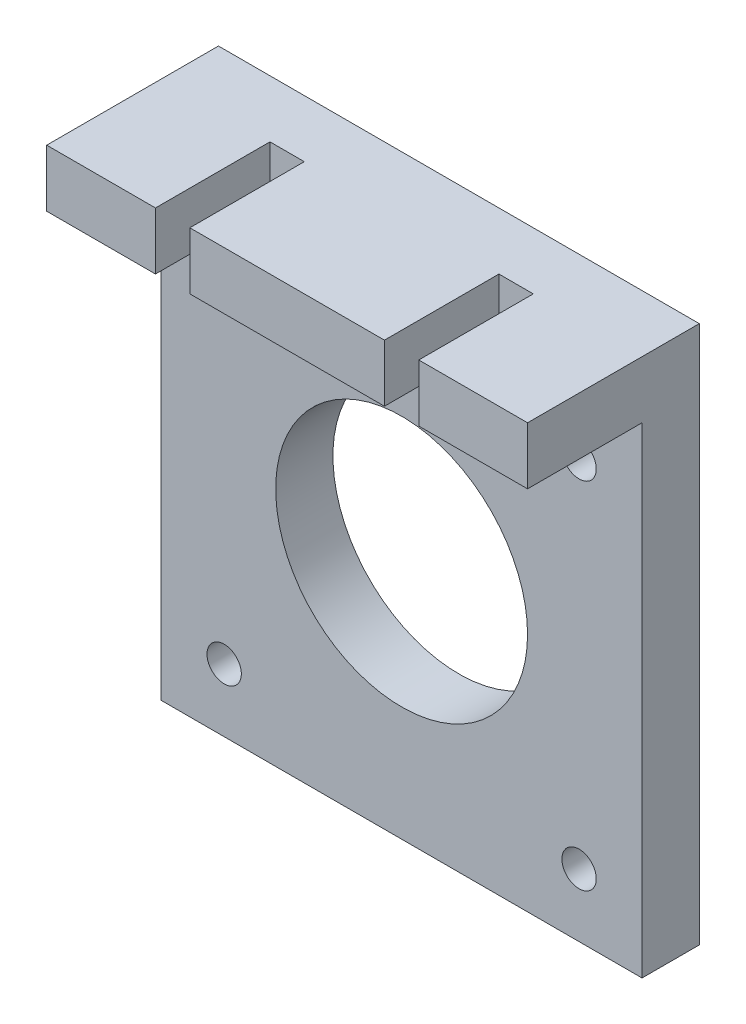
SolidWorks part; units mm, degrees
ref_plane "Front Plane" through (0, 0, 0) normal (0, 0, 1) x (1, 0, 0)
ref_plane "Top Plane" through (0, 0, 0) normal (0, 1, 0) x (1, 0, 0)
ref_plane "Right Plane" through (0, 0, 0) normal (1, 0, 0) x (0, 0, -1)
sketch "Sketch1" plane through (0, 0, 0) normal (0, 0, 1) x (1, 0, 0)
  line L0 (0, 0) -> (-26.7937, 0) construction
  line L1 (21, -21) -> (-21, -21)
  line L2 (21, -21) -> (21, 21)
  line L3 (21, 21) -> (-21, 21)
  line L4 (-21, -21) -> (-21, 21)
  line L5 (21, -21) -> (-21, 21) construction
  line L6 (21, 21) -> (-21, -21) construction
  line L7 (0, 0) -> (0, 35.2847) construction
  line L9 (-21, 21) -> (21, 21)
  line L10 (-21, 21) -> (-21, 26)
  line L11 (-21, 26) -> (21, 26)
  line L12 (21, 21) -> (21, 26)
  circle A0 centre (0, 0) radius 11
  circle A1 centre (-15.5, 15.5) radius 1.5
  circle A2 centre (-15.5, -15.5) radius 1.5
  circle A3 centre (15.5, -15.5) radius 1.5
  circle A4 centre (15.5, 15.5) radius 1.5
  point P0 (0, 0)
  dimension "D3" = 22
  dimension "D6" = 3
  dimension "D1" = 42
  dimension "D2" = 42
  dimension "D4" = 15.5
  dimension "D5" = 15.5
  dimension "D7" = 5
extrude "Boss-Extrude1" add sketch "Sketch1" along normal blind 5 contours A1 | A4 | L10 L9 L12 L11 | L2 L1 L4 L3 | A3 | A2 | A0
sketch "Sketch2" plane through (0, 0, 5) normal (0, 0, 1) x (1, 0, 0)
  line L0 (21, -21) -> (21, 26) construction
  line L1 (-21, 26) -> (21, 26)
  line L2 (-21, 26) -> (-21, 21)
  line L3 (-21, 21) -> (21, 21)
  line L4 (21, 26) -> (21, 21)
  dimension "D1" = 5
extrude "Boss-Extrude2" add sketch "Sketch2" along normal blind 10
sketch "Sketch3" plane through (0, 21, 0) normal (0, -1, 0) x (1, 0, 0)
  line L0 (0, 5) -> (0, 15.9808) construction
  line L1 (21, 5) -> (-21, 5) construction
  line L2 (-21, 15) -> (21, 15) construction
  line L3 (-11.5, 5) -> (-8.5, 5)
  line L4 (-11.5, 5) -> (-11.5, 15)
  line L5 (-11.5, 15) -> (-8.5, 15)
  line L6 (-8.5, 5) -> (-8.5, 15)
  line L7 (-21, 5) -> (21, 5) construction
  line L8 (8.5, 5) -> (11.5, 5)
  line L9 (8.5, 5) -> (8.5, 15)
  line L10 (8.5, 15) -> (11.5, 15)
  line L11 (11.5, 5) -> (11.5, 15)
  dimension "D1" = 3
  dimension "D2" = 3
  dimension "D3" = 8.5
  dimension "D4" = 8.5
extrude "Cut-Extrude1" cut sketch "Sketch3" against normal through all
